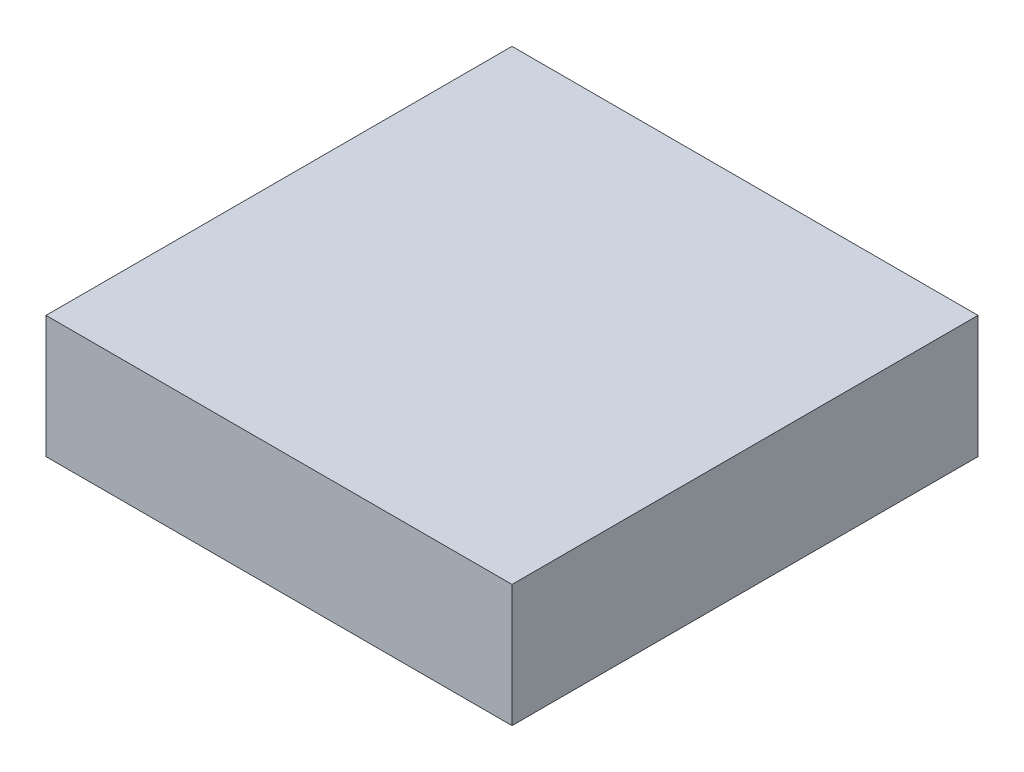
SolidWorks part; units mm, degrees
ref_plane "Front Plane" through (0, 0, 0) normal (0, 0, 1) x (1, 0, 0)
ref_plane "Top Plane" through (0, 0, 0) normal (0, 1, 0) x (1, 0, 0)
ref_plane "Right Plane" through (0, 0, 0) normal (1, 0, 0) x (0, 0, -1)
sketch "Sketch1" plane through (0, 0, 0) normal (0, 1, 0) x (1, 0, 0)
  line L1 (2, 2) -> (-2, 2)
  line L2 (2, 2) -> (2, -2)
  line L3 (2, -2) -> (-2, -2)
  line L4 (-2, 2) -> (-2, -2)
  line L5 (2, 2) -> (-2, -2) construction
  line L6 (2, -2) -> (-2, 2) construction
  point P0 (0, 0)
  dimension "D1" = 4
  dimension "D2" = 4
extrude "Boss-Extrude1" add sketch "Sketch1" along normal blind 1.05
